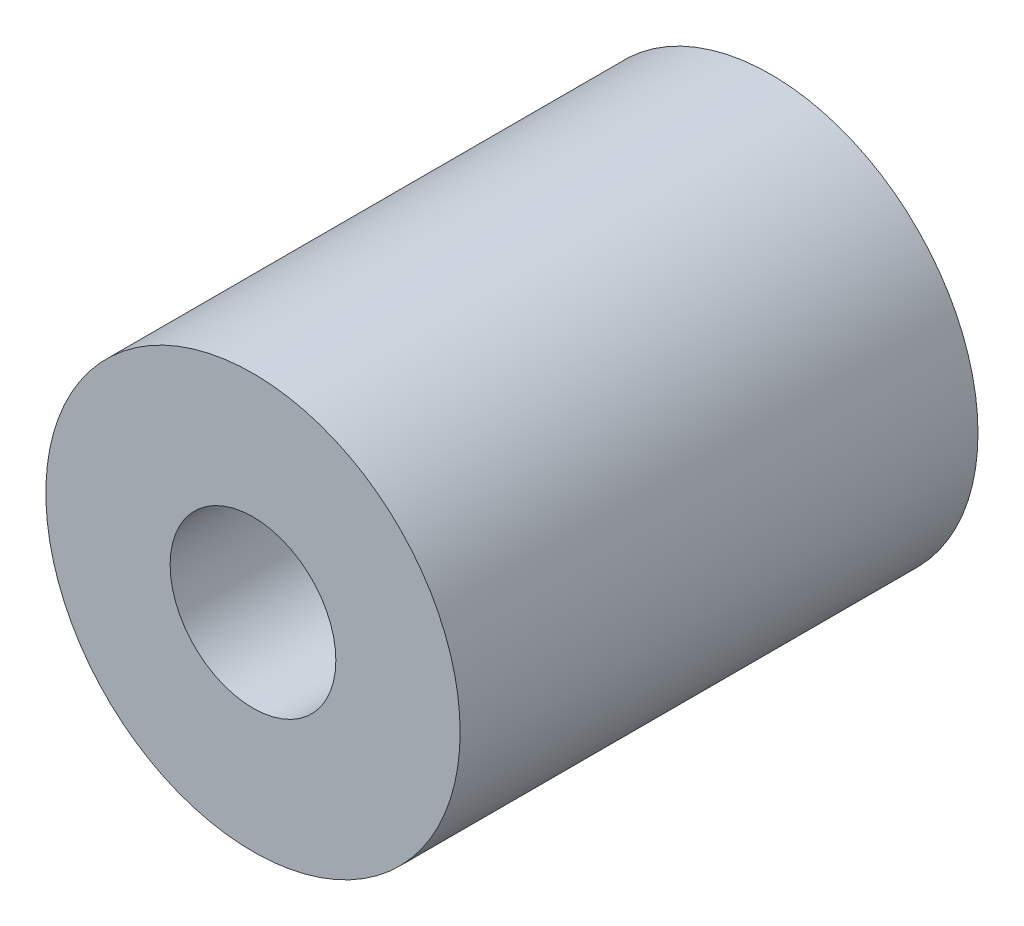
SolidWorks part; units mm, degrees
ref_plane "Ebene vorne" through (0, 0, 0) normal (0, 0, 1) x (1, 0, 0)
ref_plane "Ebene oben" through (0, 0, 0) normal (0, 1, 0) x (1, 0, 0)
ref_plane "Ebene rechts" through (0, 0, 0) normal (1, 0, 0) x (0, 0, -1)
sketch "Skizze1" plane through (0, 0, 0) normal (0, 0, 1) x (1, 0, 0)
  circle A0 centre (0, 0) radius 10
  circle A1 centre (0, 0) radius 4
  dimension "D1" = 8
  dimension "D2" = 20
extrude "Aufsatz-Linear austragen1" add sketch "Skizze1" along normal blind 25
